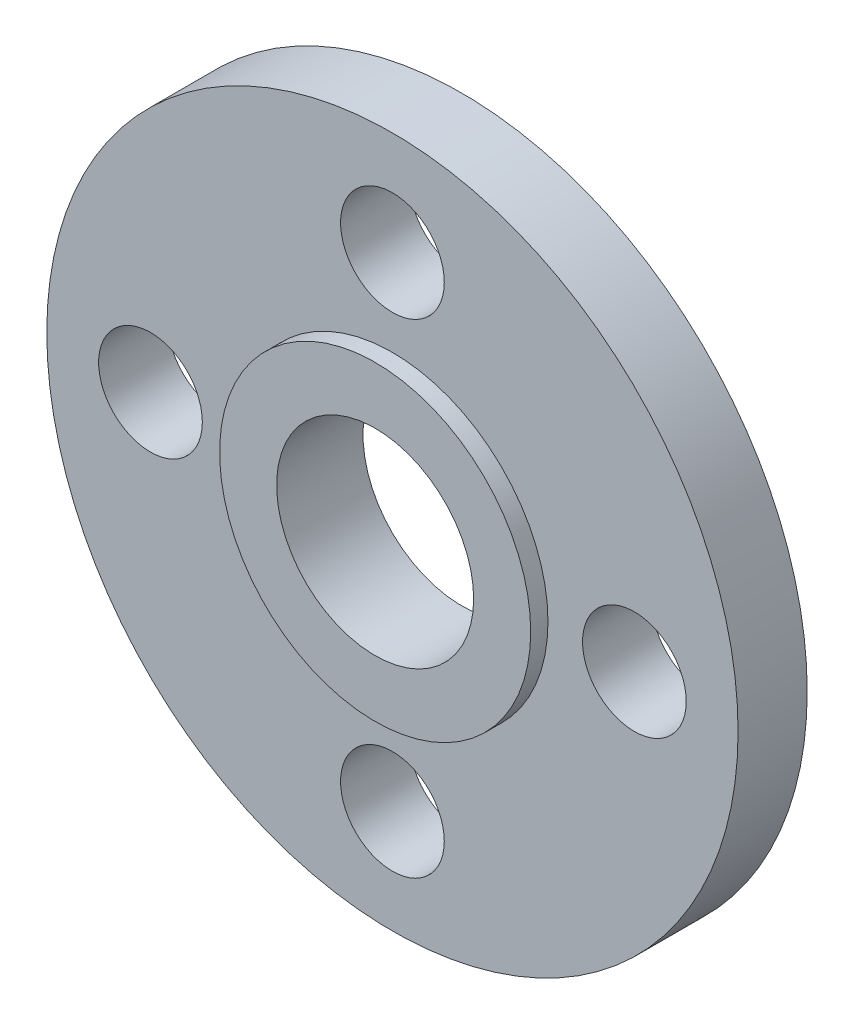
SolidWorks part; units mm, degrees
ref_plane "Plan de face" through (0, 0, 0) normal (0, 0, 1) x (1, 0, 0)
ref_plane "Plan de dessus" through (0, 0, 0) normal (0, 1, 0) x (1, 0, 0)
ref_plane "Plan de droite" through (0, 0, 0) normal (1, 0, 0) x (0, 0, -1)
sketch "Esquisse1" plane through (0, 0, 0) normal (0, 0, 1) x (1, 0, 0)
  circle A0 centre (0, 0) radius 10
  circle A1 centre (0, 0) radius 2.85
  dimension "D1" = 20
  dimension "D2" = 5.7
extrude "Boss.-Extru.1" add sketch "Esquisse1" along normal blind 2
sketch "Esquisse2" plane through (0, 0, 2) normal (0, 0, 1) x (1, 0, 0)
  circle A0 centre (0, 0) radius 4.5
  circle A1 centre (0, 0) radius 2.85 construction
  circle A2 centre (0, 0) radius 2.85
  dimension "D1" = 9
extrude "Boss.-Extru.2" add sketch "Esquisse2" along normal blind 0.5
sketch "Esquisse3" plane through (0, 0, 2) normal (0, 0, 1) x (1, 0, 0)
  circle A0 centre (0, 7) radius 1.5
  circle A1 centre (0, -7) radius 1.5
  circle A2 centre (7, 0) radius 1.5
  circle A3 centre (-7, 0) radius 1.5
  circle A4 centre (0, 0) radius 7 construction
  dimension "D1" = 3
  dimension "D2" = 14
extrude "Enlèv. mat.-Extru.1" cut sketch "Esquisse3" against normal through all
